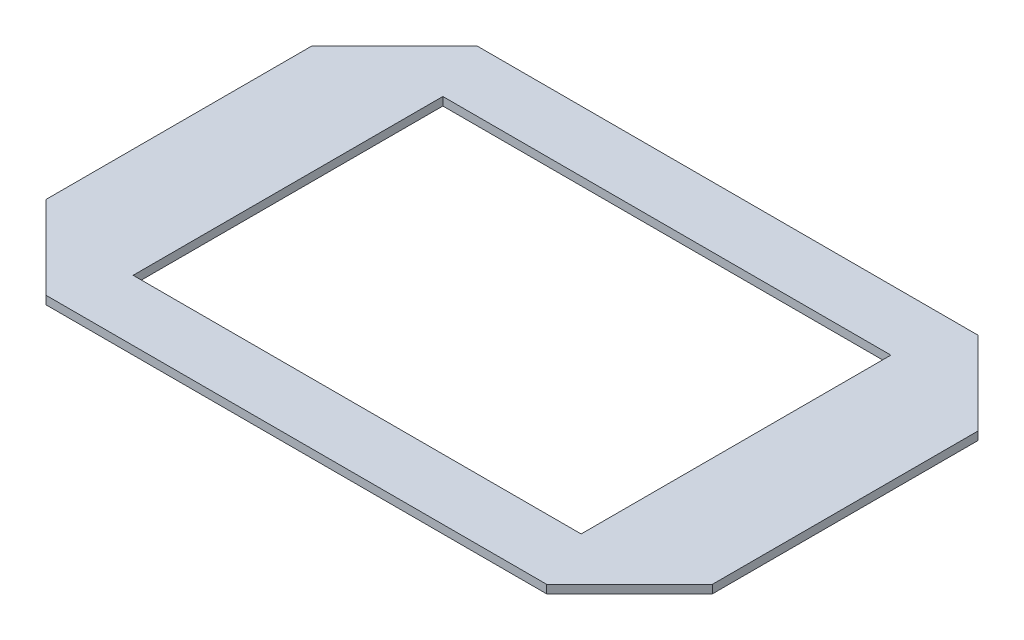
SolidWorks part; units mm, degrees
material "ABS"
ref_plane "Front Plane" through (0, 0, 0) normal (0, 0, 1) x (1, 0, 0)
ref_plane "Top Plane" through (0, 0, 0) normal (0, 1, 0) x (1, 0, 0)
ref_plane "Right Plane" through (0, 0, 0) normal (1, 0, 0) x (0, 0, -1)
sketch "Sketch1" plane through (0, 0, 0) normal (0, 1, 0) x (1, 0, 0)
  line L1 (-60.25, -39) -> (60.25, -39)
  line L2 (-60.25, -39) -> (-60.25, 39)
  line L3 (-60.25, 39) -> (60.25, 39)
  line L4 (60.25, -39) -> (60.25, 39)
  line L5 (-60.25, -39) -> (60.25, 39) construction
  line L6 (-60.25, 39) -> (60.25, -39) construction
  point P0 (0, 0)
  dimension "D1" = 120.5
  dimension "D2" = 78
extrude "Boss-Extrude1" add sketch "Sketch1" along normal blind 1.5
chamfer "Chamfer1" distance 15 angle 45 4 edges at (-60.25, 0.75, -39) (60.25, 0.75, -39) (60.25, 0.75, 39) (-60.25, 0.75, 39)
sketch "Sketch2" plane through (0, 1.5, 0) normal (0, 1, 0) x (1, 0, 0)
  line L1 (-40.5, -28) -> (40.5, -28)
  line L2 (-40.5, -28) -> (-40.5, 28)
  line L3 (-40.5, 28) -> (40.5, 28)
  line L4 (40.5, -28) -> (40.5, 28)
  line L5 (-40.5, -28) -> (40.5, 28) construction
  line L6 (-40.5, 28) -> (40.5, -28) construction
  point P0 (0, 0)
  dimension "D1" = 56
  dimension "D2" = 81
extrude "Cut-Extrude1" cut sketch "Sketch2" against normal blind 2
